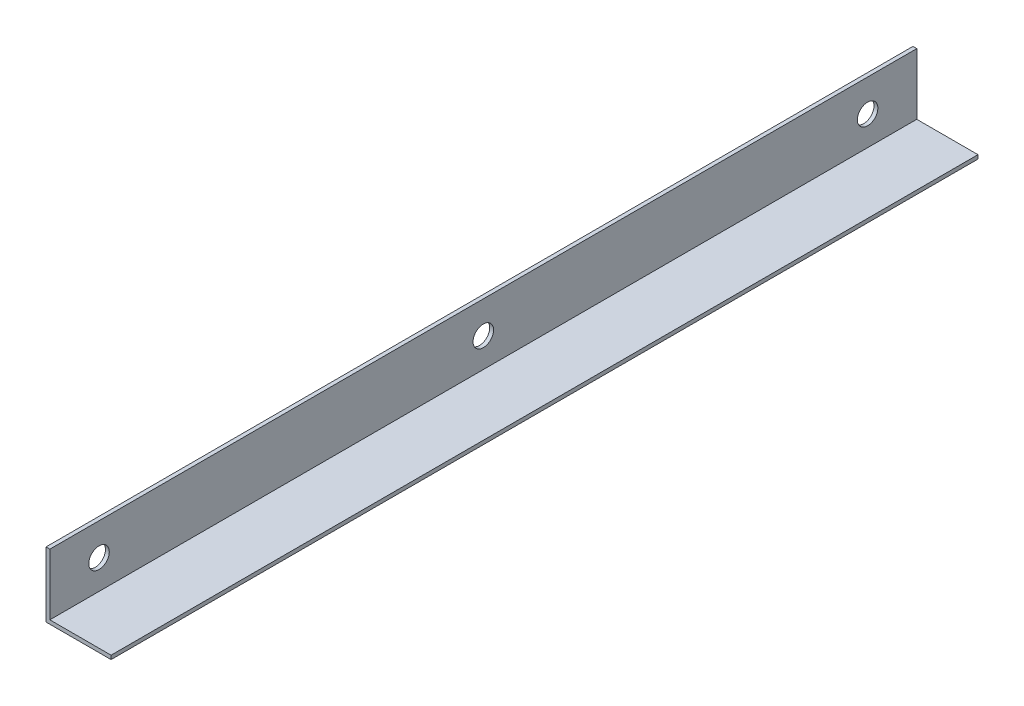
SolidWorks part; units mm, degrees
material "AISI 1015 Acero estirado en frío (SS)"
ref_plane "Alzado" through (0, 0, 0) normal (0, 0, 1) x (1, 0, 0)
ref_plane "Planta" through (0, 0, 0) normal (0, 1, 0) x (1, 0, 0)
ref_plane "Vista lateral" through (0, 0, 0) normal (1, 0, 0) x (0, 0, -1)
sketch "Croquis1" plane through (0, 0, 0) normal (0, 0, 1) x (1, 0, 0)
  line L0 (0, 0) -> (0, 25.4)
  line L1 (0, 0) -> (25.4, 0)
  line L2 (1.5, 1.5) -> (25.4, 1.5)
  line L3 (1.5, 1.5) -> (1.5, 25.4)
  line L4 (0, 25.4) -> (1.5, 25.4)
  line L5 (25.4, 1.5) -> (25.4, 0)
  dimension "D1" = 25.4
  dimension "D2" = 1.5
extrude "Saliente-Extruir1" add sketch "Croquis1" along normal blind 338.4
sketch "Croquis2" plane through (1.5, 0, 0) normal (1, 0, 0) x (0, 0, -1)
  line L0 (-169.2, 25.4) -> (-169.2, -16.8319) construction
  line L1 (-338.4, 25.4) -> (0, 25.4) construction
  line L2 (-338.4, 12.9) -> (0, 12.9) construction
  line L3 (-338.4, 1.5) -> (-338.4, 25.4) construction
  line L4 (0, 1.5) -> (0, 25.4) construction
  line L5 (-338.4, 1.5) -> (0, 1.5) construction
  circle A0 centre (-219.2, 12.9) radius 4 construction
  circle A1 centre (-119.2, 12.9) radius 4 construction
  circle A2 centre (-19.2, 12.9) radius 4
  circle A3 centre (-319.2, 12.9) radius 4
  circle A4 centre (-169.2, 12.9) radius 4
  dimension "D6" = 8
  dimension "D1" = 11.4
  dimension "D2" = 50
  dimension "D3" = 50
  dimension "D4" = 100
  dimension "D5" = 100
extrude "Cortar-Extruir1" cut sketch "Croquis2" against normal blind 2
